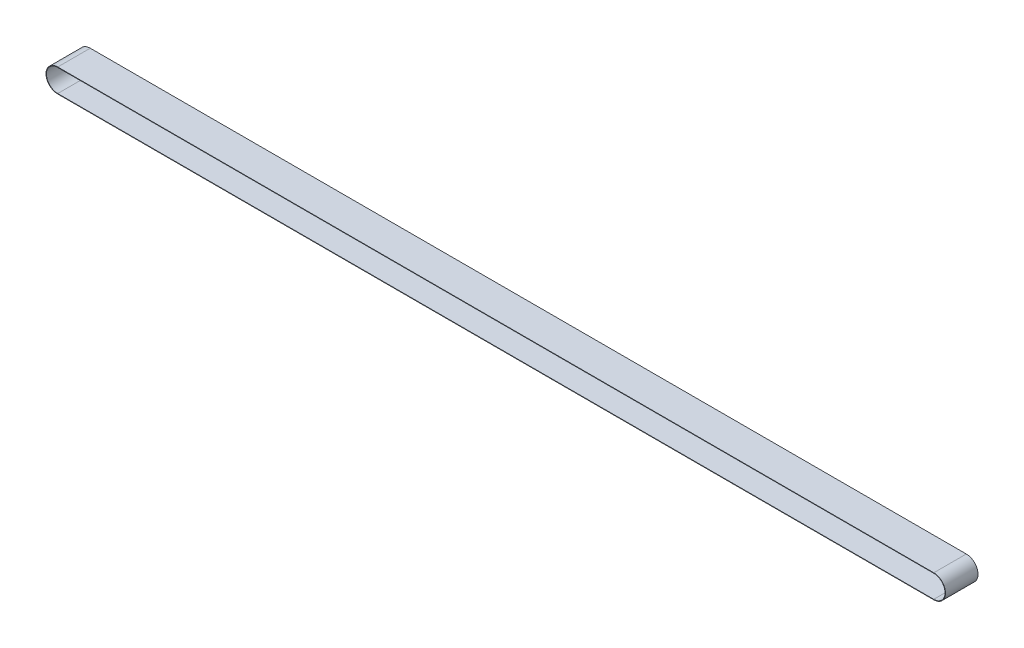
SolidWorks part; units mm, degrees
material "尼龙(黑)"
ref_plane "前视基准面" through (0, 0, 0) normal (0, 0, 1) x (1, 0, 0)
ref_plane "上视基准面" through (0, 0, 0) normal (0, 1, 0) x (1, 0, 0)
ref_plane "右视基准面" through (0, 0, 0) normal (1, 0, 0) x (0, 0, -1)
sketch "草图1" plane through (0, 0, 0) normal (0, 0, 1) x (1, 0, 0)
  line L0 (-1010, 0) -> (1010, 0) construction
  line L1 (-1010, 26) -> (1010, 26)
  line L2 (-1010, -26) -> (1010, -26)
  arc A0 (-1010, 26) -> (-1010, -26) centre (-1010, 0) ccw
  arc A1 (1010, -26) -> (1010, 26) centre (1010, 0) ccw
  point P3 (0, 0)
  dimension "D1" = 26
  dimension "D2" = 2020
extrude "拉伸-薄壁1" add sketch "草图1" along normal mid plane 75 thin contours L1 A1 L2 A0 thin type one direction wall 1
equation "\"长度\"=2020"
